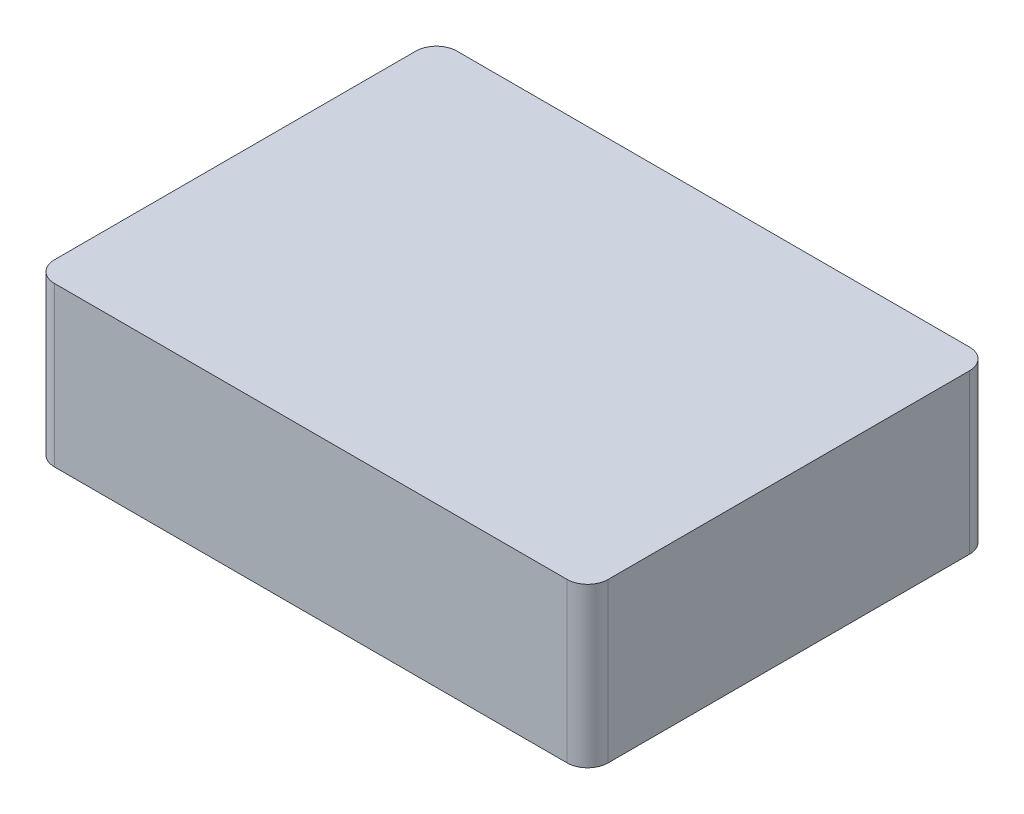
SolidWorks part; units mm, degrees
ref_plane "Front Plane" through (0, 0, 0) normal (0, 0, 1) x (1, 0, 0)
ref_plane "Top Plane" through (0, 0, 0) normal (0, 1, 0) x (1, 0, 0)
ref_plane "Right Plane" through (0, 0, 0) normal (1, 0, 0) x (0, 0, -1)
sketch "Sketch1" plane through (0, 0, 0) normal (0, 1, 0) x (1, 0, 0)
  line L1 (0, 0) -> (54, 0)
  line L2 (0, 0) -> (0, 39.25)
  line L3 (0, 39.25) -> (54, 39.25)
  line L4 (54, 0) -> (54, 39.25)
  dimension "D1" = 54
  dimension "D2" = 39.25
extrude "Boss-Extrude1" add sketch "Sketch1" along normal blind 15.5
fillet "Fillet1" radius 2 1 edges at (0, 7.75, 0)
fillet "Fillet2" radius 2 3 edges at (54, 7.75, -39.25) (54, 7.75, 0) (0, 7.75, -39.25)
